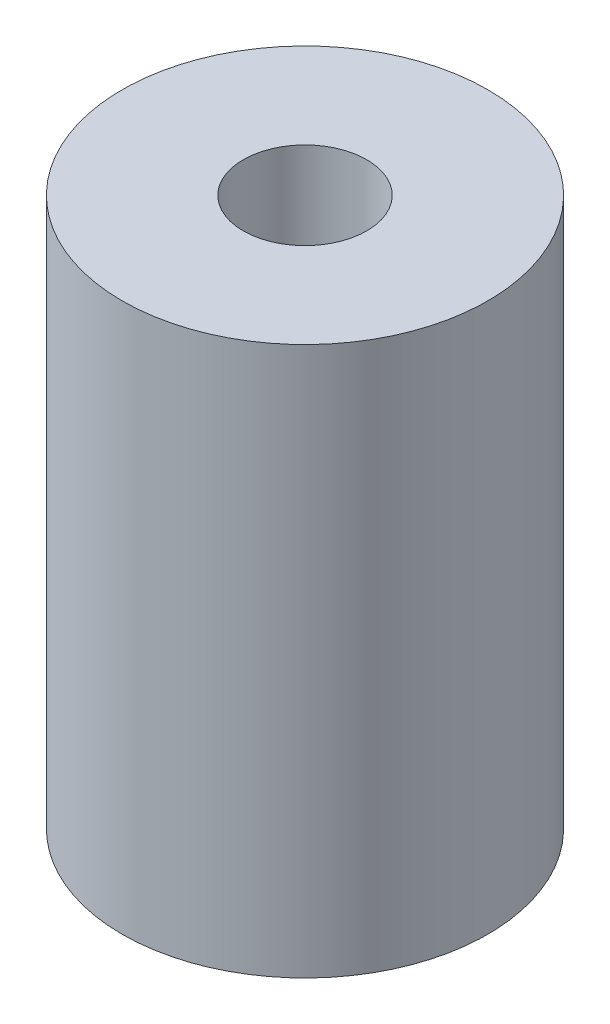
SolidWorks part; units mm, degrees
ref_plane "Front Plane" through (0, 0, 0) normal (0, 0, 1) x (1, 0, 0)
ref_plane "Top Plane" through (0, 0, 0) normal (0, 1, 0) x (1, 0, 0)
ref_plane "Right Plane" through (0, 0, 0) normal (1, 0, 0) x (0, 0, -1)
sketch "Sketch1" plane through (0, 0, 0) normal (0, 1, 0) x (1, 0, 0)
  circle A0 centre (0, 0) radius 4
  circle A1 centre (0, 0) radius 1.35
extrude "Boss-Extrude1" add sketch "Sketch1" along normal blind 12
